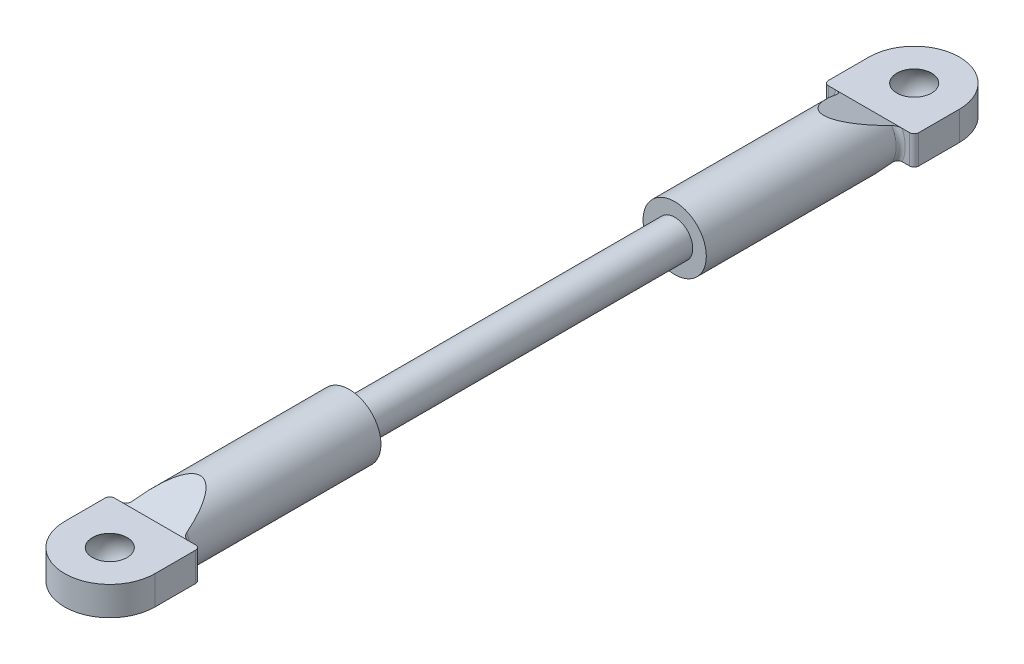
SolidWorks part; units mm, degrees
ref_plane "Front Plane" through (0, 0, 0) normal (0, 0, 1) x (1, 0, 0)
ref_plane "Top Plane" through (0, 0, 0) normal (0, 1, 0) x (1, 0, 0)
ref_plane "Right Plane" through (0, 0, 0) normal (1, 0, 0) x (0, 0, -1)
sketch "Sketch1" plane through (0, 0, 0) normal (0, 0, 1) x (1, 0, 0)
  circle A0 centre (0, 0) radius 2
  dimension "D1" = 4
extrude "Screw Section" add sketch "Sketch1" along normal blind 18 contours A0
sketch "Sketch2" plane through (0, 0, 18) normal (0, 0, 1) x (1, 0, 0)
  circle A0 centre (0, 0) radius 3.5
  dimension "D1" = 7
extrude "Bar Section" add sketch "Sketch2" along normal blind 21.5
sketch "Sketch3" plane through (0, 0, 0) normal (0, 1, 0) x (1, 0, 0)
  line L0 (5, -39.5) -> (-5, -39.5)
  line L1 (-5, -39.5) -> (-5, -44.5)
  line L2 (5, -39.5) -> (5, -44.5)
  line L3 (-3.5, -39.5) -> (3.5, -39.5) construction
  arc A0 (-5, -44.5) -> (5, -44.5) centre (0, -44.5) ccw
  point P4 (0, -49.5)
  dimension "D1" = 5
  dimension "D2" = 10
  dimension "D3" = 10
extrude "Mount Section" add sketch "Sketch3" along normal mid plane 3.2
sketch "Sketch4" plane through (0, 0, 0) normal (1, 0, 0) x (0, 0, -1)
  line L0 (-34.5, -3.5) -> (-39.5, -1.6)
  line L1 (-39.5, -3.5) -> (-18, -3.5) construction
  line L2 (-39.5, -1.6) -> (-39.5, -3.5)
  line L3 (-39.5, -1.6) -> (-39.5, -3.5) construction
  line L4 (-39.5, -3.5) -> (-34.5, -3.5)
  line L5 (-34.5, 3.5) -> (-39.5, 1.6)
  line L6 (-39.5, 3.5) -> (-39.5, 1.6) construction
  line L7 (-39.5, 3.5) -> (-34.5, 3.5)
  line L9 (-39.5, 1.6) -> (-39.5, 3.5)
  dimension "D1" = 5
  dimension "D2" = 1.9
extrude "Bar Taper" cut sketch "Sketch4" against normal through all both and the other way through all
fillet "Mount Fillet" radius 0.5 4 edges at (-5, 0, 39.5) (3.5, 0, 39.5) (-3.5, 0, 39.5) (5, 0, 39.5)
sketch "Sketch6" plane through (0, 0, 0) normal (1, 0, 0) x (0, 0, -1)
  line L0 (-44.5, 1.6) -> (-44.5, -1.6) construction
  line L1 (-49.5, -1.6) -> (-44.5, -1.6) construction
  line L2 (-44.5, 1.6) -> (-49.5, 1.6) construction
  line L4 (-46.4209, -1.6) -> (-44.5, -1.6)
  line L5 (-44.5, -1.6) -> (-44.5, 1.6)
  line L6 (-44.5, 1.6) -> (-46.4209, 1.6)
  arc A0 (-46.4209, -1.6) -> (-46.4209, 1.6) centre (-44.5, 0) cw
  dimension "D1" = 2.5
revolve "Ball Hole" cut sketch "Sketch6" angle 360 about L5
mirror "Mirror" of "Ball Hole", "Bar Section", "Bar Taper", "Mount Section", "Mount Fillet", "Screw Section"
ref_point "Point1"
ref_point "Point2"
